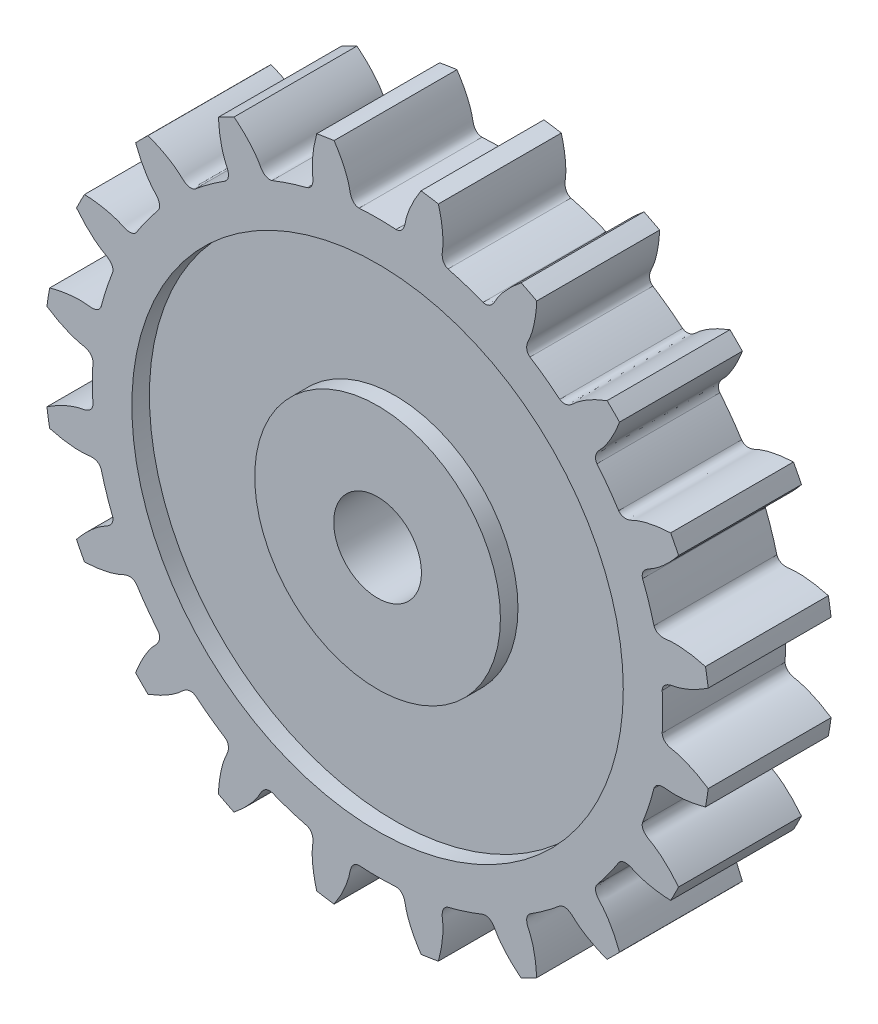
SolidWorks part; units mm, degrees
ref_plane "Alzado" through (0, 0, 0) normal (0, 0, 1) x (1, 0, 0)
ref_plane "Planta" through (0, 0, 0) normal (0, 1, 0) x (1, 0, 0)
ref_plane "Vista lateral" through (0, 0, 0) normal (1, 0, 0) x (0, 0, -1)
sketch "Croquis1" plane through (0, 0, 0) normal (0, 0, 1) x (1, 0, 0)
  line L0 (0, 0) -> (0, 22.9877) construction
  line L1 (0, 0) -> (13.435, 13.435) construction
  circle A0 centre (0, 0) radius 14 construction
  circle A1 centre (0, 0) radius 19 construction
  arc A2 (6.0093, 15.098) -> (4.0127, 15.7468) centre (0, 0) ccw
  arc A3 (17.1503, 8.1773) -> (16.6963, 9.0683) centre (0, 0) ccw
  arc A4 (18.8378, 2.4774) -> (18.6814, 3.4651) centre (0, 0) ccw
  arc A5 (18.6814, -3.4651) -> (18.8378, -2.4774) centre (0, 0) ccw
  arc A6 (16.6963, -9.0683) -> (17.1503, -8.1773) centre (0, 0) ccw
  arc A7 (13.0768, -13.7839) -> (13.7839, -13.0768) centre (0, 0) ccw
  arc A8 (8.1773, -17.1503) -> (9.0683, -16.6963) centre (0, 0) ccw
  arc A9 (2.4774, -18.8378) -> (3.4651, -18.6814) centre (0, 0) ccw
  arc A10 (-3.4651, -18.6814) -> (-2.4774, -18.8378) centre (0, 0) ccw
  arc A11 (-9.0683, -16.6963) -> (-8.1773, -17.1503) centre (0, 0) ccw
  arc A12 (-13.7839, -13.0768) -> (-13.0768, -13.7839) centre (0, 0) ccw
  arc A13 (-17.1503, -8.1773) -> (-16.6963, -9.0683) centre (0, 0) ccw
  arc A14 (-18.8378, -2.4774) -> (-18.6814, -3.4651) centre (0, 0) ccw
  arc A15 (-18.6814, 3.4651) -> (-18.8378, 2.4774) centre (0, 0) ccw
  arc A16 (-16.6963, 9.0683) -> (-17.1503, 8.1773) centre (0, 0) ccw
  arc A17 (-13.0768, 13.7839) -> (-13.7839, 13.0768) centre (0, 0) ccw
  arc A18 (-8.1773, 17.1503) -> (-9.0683, 16.6963) centre (0, 0) ccw
  arc A19 (-2.4774, 18.8378) -> (-3.4651, 18.6814) centre (0, 0) ccw
  arc A20 (3.4651, 18.6814) -> (2.4774, 18.8378) centre (0, 0) ccw
  arc A21 (9.0683, 16.6963) -> (8.1773, 17.1503) centre (0, 0) ccw
  arc A22 (10.3808, 12.5021) -> (8.6824, 13.7361) centre (0, 0) ccw
  arc A23 (13.7361, 8.6824) -> (12.5021, 10.3808) centre (0, 0) ccw
  arc A24 (15.7468, 4.0127) -> (15.098, 6.0093) centre (0, 0) ccw
  arc A25 (16.2161, -1.0497) -> (16.2161, 1.0497) centre (0, 0) ccw
  arc A26 (15.098, -6.0093) -> (15.7468, -4.0127) centre (0, 0) ccw
  arc A27 (12.5021, -10.3808) -> (13.7361, -8.6824) centre (0, 0) ccw
  arc A28 (8.6824, -13.7361) -> (10.3808, -12.5021) centre (0, 0) ccw
  arc A29 (4.0127, -15.7468) -> (6.0093, -15.098) centre (0, 0) ccw
  arc A30 (-1.0497, -16.2161) -> (1.0497, -16.2161) centre (0, 0) ccw
  arc A31 (-6.0093, -15.098) -> (-4.0127, -15.7468) centre (0, 0) ccw
  arc A32 (-10.3808, -12.5021) -> (-8.6824, -13.7361) centre (0, 0) ccw
  arc A33 (-13.7361, -8.6824) -> (-12.5021, -10.3808) centre (0, 0) ccw
  arc A34 (-15.7468, -4.0127) -> (-15.098, -6.0093) centre (0, 0) ccw
  arc A35 (-16.2161, 1.0497) -> (-16.2161, -1.0497) centre (0, 0) ccw
  arc A36 (-15.098, 6.0093) -> (-15.7468, 4.0127) centre (0, 0) ccw
  arc A37 (-12.5021, 10.3808) -> (-13.7361, 8.6824) centre (0, 0) ccw
  arc A38 (-8.6824, 13.7361) -> (-10.3808, 12.5021) centre (0, 0) ccw
  arc A39 (-4.0127, 15.7468) -> (-6.0093, 15.098) centre (0, 0) ccw
  arc A40 (1.0497, 16.2161) -> (-1.0497, 16.2161) centre (0, 0) ccw
  circle A41 centre (0, 0) radius 2.5
  arc A114 (13.7839, 13.0768) -> (13.0768, 13.7839) centre (0, 0) ccw
  spline S0 degree 3 poles (16.6963, 9.0683) (16.527, 9.0609) (16.2672, 9.0419) (15.9256, 8.9993) (15.6776, 8.9589) (15.4527, 8.9136) (15.2508, 8.8651) (15.072, 8.815) (14.9159, 8.7649) (14.7823, 8.7166) (14.671, 8.6714) (14.5901, 8.6353) (14.5356, 8.6086) (14.4998, 8.5913) (14.4673, 8.5768) (14.4142, 8.5546) (14.3398, 8.5283) (14.2409, 8.5042) (14.1356, 8.4929) (14.0177, 8.5009) (13.8695, 8.5484) (13.7779, 8.6259) (13.7361, 8.6824) knots 0 0 0 0 0.158673 0.243949 0.322403 0.394035 0.458845 0.516832 0.567998 0.612341 0.649863 0.680562 0.695323 0.706671 0.717793 0.728713 0.760516 0.791693 0.823807 0.859359 0.901681 0.967655 0.967655 0.967655 0.967655
  spline S1 degree 3 poles (15.098, 6.0093) (15.0769, 6.0764) (15.068, 6.196) (15.1168, 6.3439) (15.1796, 6.444) (15.2507, 6.5225) (15.3282, 6.5883) (15.3933, 6.6331) (15.4424, 6.663) (15.4733, 6.6807) (15.5083, 6.6995) (15.5619, 6.7279) (15.6387, 6.7721) (15.7407, 6.8357) (15.8583, 6.9153) (15.9905, 7.0122) (16.1362, 7.1274) (16.2941, 7.2622) (16.4629, 7.4175) (16.6414, 7.5944) (16.8767, 7.8457) (17.0448, 8.0448) (17.1503, 8.1773) knots 0.032345 0.032345 0.032345 0.032345 0.098319 0.140641 0.176193 0.208307 0.239484 0.271287 0.282207 0.293329 0.304677 0.319438 0.350137 0.387659 0.432002 0.483168 0.541155 0.605965 0.677597 0.756051 0.841327 1 1 1 1
  spline S2 degree 3 poles (18.6814, 3.4651) (18.5181, 3.5103) (18.2651, 3.5726) (17.9271, 3.6375) (17.6787, 3.6758) (17.4508, 3.7022) (17.2438, 3.7184) (17.0583, 3.726) (16.8944, 3.7266) (16.7524, 3.7219) (16.6325, 3.7134) (16.5444, 3.7041) (16.4844, 3.6955) (16.445, 3.6901) (16.4096, 3.6864) (16.3523, 3.6817) (16.2733, 3.6796) (16.1719, 3.6873) (16.0682, 3.709) (15.9586, 3.7532) (15.8322, 3.8441) (15.7691, 3.9461) (15.7468, 4.0127) knots 0 0 0 0 0.158673 0.243949 0.322403 0.394035 0.458845 0.516832 0.567998 0.612341 0.649863 0.680562 0.695323 0.706671 0.717793 0.728713 0.760516 0.791693 0.823807 0.859359 0.901681 0.967655 0.967655 0.967655 0.967655
  spline S3 degree 3 poles (16.2161, 1.0497) (16.2167, 1.1199) (16.2452, 1.2365) (16.3373, 1.362) (16.4279, 1.4378) (16.5198, 1.4905) (16.6139, 1.5292) (16.6896, 1.5516) (16.7456, 1.5649) (16.7805, 1.5723) (16.8196, 1.5793) (16.8793, 1.5897) (16.966, 1.608) (17.0826, 1.637) (17.2191, 1.6764) (17.3748, 1.7276) (17.5489, 1.7922) (17.7407, 1.8716) (17.9493, 1.9672) (18.1737, 2.0803) (18.4751, 2.2465) (18.6965, 2.3839) (18.8378, 2.4774) knots 0.032345 0.032345 0.032345 0.032345 0.098319 0.140641 0.176193 0.208307 0.239484 0.271287 0.282207 0.293329 0.304677 0.319438 0.350137 0.387659 0.432002 0.483168 0.541155 0.605965 0.677597 0.756051 0.841327 1 1 1 1
  spline S4 degree 3 poles (18.8378, -2.4774) (18.6965, -2.3839) (18.4751, -2.2465) (18.1737, -2.0803) (17.9493, -1.9672) (17.7407, -1.8716) (17.5489, -1.7922) (17.3748, -1.7276) (17.2191, -1.6764) (17.0826, -1.637) (16.966, -1.608) (16.8793, -1.5897) (16.8196, -1.5793) (16.7805, -1.5723) (16.7456, -1.5649) (16.6896, -1.5516) (16.6139, -1.5292) (16.5198, -1.4905) (16.4279, -1.4378) (16.3373, -1.362) (16.2452, -1.2365) (16.2167, -1.1199) (16.2161, -1.0497) knots 0 0 0 0 0.158673 0.243949 0.322403 0.394035 0.458845 0.516832 0.567998 0.612341 0.649863 0.680562 0.695323 0.706671 0.717793 0.728713 0.760516 0.791693 0.823807 0.859359 0.901681 0.967655 0.967655 0.967655 0.967655
  spline S5 degree 3 poles (15.7468, -4.0127) (15.7691, -3.9461) (15.8322, -3.8441) (15.9586, -3.7532) (16.0682, -3.709) (16.1719, -3.6873) (16.2733, -3.6796) (16.3523, -3.6817) (16.4096, -3.6864) (16.445, -3.6901) (16.4844, -3.6955) (16.5444, -3.7041) (16.6325, -3.7134) (16.7524, -3.7219) (16.8944, -3.7266) (17.0583, -3.726) (17.2438, -3.7184) (17.4508, -3.7022) (17.6787, -3.6758) (17.9271, -3.6375) (18.2651, -3.5726) (18.5181, -3.5103) (18.6814, -3.4651) knots 0.032345 0.032345 0.032345 0.032345 0.098319 0.140641 0.176193 0.208307 0.239484 0.271287 0.282207 0.293329 0.304677 0.319438 0.350137 0.387659 0.432002 0.483168 0.541155 0.605965 0.677597 0.756051 0.841327 1 1 1 1
  spline S6 degree 3 poles (17.1503, -8.1773) (17.0448, -8.0448) (16.8767, -7.8457) (16.6414, -7.5944) (16.4629, -7.4175) (16.2941, -7.2622) (16.1362, -7.1274) (15.9905, -7.0122) (15.8583, -6.9153) (15.7407, -6.8357) (15.6387, -6.7721) (15.5619, -6.7279) (15.5083, -6.6995) (15.4733, -6.6807) (15.4424, -6.663) (15.3933, -6.6331) (15.3282, -6.5883) (15.2507, -6.5225) (15.1796, -6.444) (15.1168, -6.3439) (15.068, -6.196) (15.0769, -6.0764) (15.098, -6.0093) knots 0 0 0 0 0.158673 0.243949 0.322403 0.394035 0.458845 0.516832 0.567998 0.612341 0.649863 0.680562 0.695323 0.706671 0.717793 0.728713 0.760516 0.791693 0.823807 0.859359 0.901681 0.967655 0.967655 0.967655 0.967655
  spline S7 degree 3 poles (13.7361, -8.6824) (13.7779, -8.6259) (13.8695, -8.5484) (14.0177, -8.5009) (14.1356, -8.4929) (14.2409, -8.5042) (14.3398, -8.5283) (14.4142, -8.5546) (14.4673, -8.5768) (14.4998, -8.5913) (14.5356, -8.6086) (14.5901, -8.6353) (14.671, -8.6714) (14.7823, -8.7166) (14.9159, -8.7649) (15.072, -8.815) (15.2508, -8.8651) (15.4527, -8.9136) (15.6776, -8.9589) (15.9256, -8.9993) (16.2672, -9.0419) (16.527, -9.0609) (16.6963, -9.0683) knots 0.032345 0.032345 0.032345 0.032345 0.098319 0.140641 0.176193 0.208307 0.239484 0.271287 0.282207 0.293329 0.304677 0.319438 0.350137 0.387659 0.432002 0.483168 0.541155 0.605965 0.677597 0.756051 0.841327 1 1 1 1
  spline S8 degree 3 poles (13.7839, -13.0768) (13.7246, -12.9182) (13.6262, -12.6769) (13.4801, -12.3652) (13.365, -12.1418) (13.2525, -11.9419) (13.1439, -11.7649) (13.041, -11.6103) (12.9452, -11.4774) (12.8579, -11.3653) (12.7806, -11.2733) (12.7212, -11.2075) (12.679, -11.164) (12.6515, -11.1353) (12.6276, -11.1088) (12.5902, -11.0652) (12.5421, -11.0025) (12.4887, -10.916) (12.4453, -10.8193) (12.4166, -10.7047) (12.4159, -10.5491) (12.4613, -10.438) (12.5021, -10.3808) knots 0 0 0 0 0.158673 0.243949 0.322403 0.394035 0.458845 0.516832 0.567998 0.612341 0.649863 0.680562 0.695323 0.706671 0.717793 0.728713 0.760516 0.791693 0.823807 0.859359 0.901681 0.967655 0.967655 0.967655 0.967655
  spline S9 degree 3 poles (10.3808, -12.5021) (10.438, -12.4613) (10.5491, -12.4159) (10.7047, -12.4166) (10.8193, -12.4453) (10.916, -12.4887) (11.0025, -12.5421) (11.0652, -12.5902) (11.1088, -12.6276) (11.1353, -12.6515) (11.164, -12.679) (11.2075, -12.7212) (11.2733, -12.7806) (11.3653, -12.8579) (11.4774, -12.9452) (11.6103, -13.041) (11.7649, -13.1439) (11.9419, -13.2525) (12.1418, -13.365) (12.3652, -13.4801) (12.6769, -13.6262) (12.9182, -13.7246) (13.0768, -13.7839) knots 0.032345 0.032345 0.032345 0.032345 0.098319 0.140641 0.176193 0.208307 0.239484 0.271287 0.282207 0.293329 0.304677 0.319438 0.350137 0.387659 0.432002 0.483168 0.541155 0.605965 0.677597 0.756051 0.841327 1 1 1 1
  spline S10 degree 3 poles (9.0683, -16.6963) (9.0609, -16.527) (9.0419, -16.2672) (8.9993, -15.9256) (8.9589, -15.6776) (8.9136, -15.4527) (8.8651, -15.2508) (8.815, -15.072) (8.7649, -14.9159) (8.7166, -14.7823) (8.6714, -14.671) (8.6353, -14.5901) (8.6086, -14.5356) (8.5913, -14.4998) (8.5768, -14.4673) (8.5546, -14.4142) (8.5283, -14.3398) (8.5042, -14.2409) (8.4929, -14.1356) (8.5009, -14.0177) (8.5484, -13.8695) (8.6259, -13.7779) (8.6824, -13.7361) knots 0 0 0 0 0.158673 0.243949 0.322403 0.394035 0.458845 0.516832 0.567998 0.612341 0.649863 0.680562 0.695323 0.706671 0.717793 0.728713 0.760516 0.791693 0.823807 0.859359 0.901681 0.967655 0.967655 0.967655 0.967655
  spline S11 degree 3 poles (6.0093, -15.098) (6.0764, -15.0769) (6.196, -15.068) (6.3439, -15.1168) (6.444, -15.1796) (6.5225, -15.2507) (6.5883, -15.3282) (6.6331, -15.3933) (6.663, -15.4424) (6.6807, -15.4733) (6.6995, -15.5083) (6.7279, -15.5619) (6.7721, -15.6387) (6.8357, -15.7407) (6.9153, -15.8583) (7.0122, -15.9905) (7.1274, -16.1362) (7.2622, -16.2941) (7.4175, -16.4629) (7.5944, -16.6414) (7.8457, -16.8767) (8.0448, -17.0448) (8.1773, -17.1503) knots 0.032345 0.032345 0.032345 0.032345 0.098319 0.140641 0.176193 0.208307 0.239484 0.271287 0.282207 0.293329 0.304677 0.319438 0.350137 0.387659 0.432002 0.483168 0.541155 0.605965 0.677597 0.756051 0.841327 1 1 1 1
  spline S12 degree 3 poles (3.4651, -18.6814) (3.5103, -18.5181) (3.5726, -18.2651) (3.6375, -17.9271) (3.6758, -17.6787) (3.7022, -17.4508) (3.7184, -17.2438) (3.726, -17.0583) (3.7266, -16.8944) (3.7219, -16.7524) (3.7134, -16.6325) (3.7041, -16.5444) (3.6955, -16.4844) (3.6901, -16.445) (3.6864, -16.4096) (3.6817, -16.3523) (3.6796, -16.2733) (3.6873, -16.1719) (3.709, -16.0682) (3.7532, -15.9586) (3.8441, -15.8322) (3.9461, -15.7691) (4.0127, -15.7468) knots 0 0 0 0 0.158673 0.243949 0.322403 0.394035 0.458845 0.516832 0.567998 0.612341 0.649863 0.680562 0.695323 0.706671 0.717793 0.728713 0.760516 0.791693 0.823807 0.859359 0.901681 0.967655 0.967655 0.967655 0.967655
  spline S13 degree 3 poles (1.0497, -16.2161) (1.1199, -16.2167) (1.2365, -16.2452) (1.362, -16.3373) (1.4378, -16.4279) (1.4905, -16.5198) (1.5292, -16.6139) (1.5516, -16.6896) (1.5649, -16.7456) (1.5723, -16.7805) (1.5793, -16.8196) (1.5897, -16.8793) (1.608, -16.966) (1.637, -17.0826) (1.6764, -17.2191) (1.7276, -17.3748) (1.7922, -17.5489) (1.8716, -17.7407) (1.9672, -17.9493) (2.0803, -18.1737) (2.2465, -18.4751) (2.3839, -18.6965) (2.4774, -18.8378) knots 0.032345 0.032345 0.032345 0.032345 0.098319 0.140641 0.176193 0.208307 0.239484 0.271287 0.282207 0.293329 0.304677 0.319438 0.350137 0.387659 0.432002 0.483168 0.541155 0.605965 0.677597 0.756051 0.841327 1 1 1 1
  spline S14 degree 3 poles (-2.4774, -18.8378) (-2.3839, -18.6965) (-2.2465, -18.4751) (-2.0803, -18.1737) (-1.9672, -17.9493) (-1.8716, -17.7407) (-1.7922, -17.5489) (-1.7276, -17.3748) (-1.6764, -17.2191) (-1.637, -17.0826) (-1.608, -16.966) (-1.5897, -16.8793) (-1.5793, -16.8196) (-1.5723, -16.7805) (-1.5649, -16.7456) (-1.5516, -16.6896) (-1.5292, -16.6139) (-1.4905, -16.5198) (-1.4378, -16.4279) (-1.362, -16.3373) (-1.2365, -16.2452) (-1.1199, -16.2167) (-1.0497, -16.2161) knots 0 0 0 0 0.158673 0.243949 0.322403 0.394035 0.458845 0.516832 0.567998 0.612341 0.649863 0.680562 0.695323 0.706671 0.717793 0.728713 0.760516 0.791693 0.823807 0.859359 0.901681 0.967655 0.967655 0.967655 0.967655
  spline S15 degree 3 poles (-4.0127, -15.7468) (-3.9461, -15.7691) (-3.8441, -15.8322) (-3.7532, -15.9586) (-3.709, -16.0682) (-3.6873, -16.1719) (-3.6796, -16.2733) (-3.6817, -16.3523) (-3.6864, -16.4096) (-3.6901, -16.445) (-3.6955, -16.4844) (-3.7041, -16.5444) (-3.7134, -16.6325) (-3.7219, -16.7524) (-3.7266, -16.8944) (-3.726, -17.0583) (-3.7184, -17.2438) (-3.7022, -17.4508) (-3.6758, -17.6787) (-3.6375, -17.9271) (-3.5726, -18.2651) (-3.5103, -18.5181) (-3.4651, -18.6814) knots 0.032345 0.032345 0.032345 0.032345 0.098319 0.140641 0.176193 0.208307 0.239484 0.271287 0.282207 0.293329 0.304677 0.319438 0.350137 0.387659 0.432002 0.483168 0.541155 0.605965 0.677597 0.756051 0.841327 1 1 1 1
  spline S16 degree 3 poles (-8.1773, -17.1503) (-8.0448, -17.0448) (-7.8457, -16.8767) (-7.5944, -16.6414) (-7.4175, -16.4629) (-7.2622, -16.2941) (-7.1274, -16.1362) (-7.0122, -15.9905) (-6.9153, -15.8583) (-6.8357, -15.7407) (-6.7721, -15.6387) (-6.7279, -15.5619) (-6.6995, -15.5083) (-6.6807, -15.4733) (-6.663, -15.4424) (-6.6331, -15.3933) (-6.5883, -15.3282) (-6.5225, -15.2507) (-6.444, -15.1796) (-6.3439, -15.1168) (-6.196, -15.068) (-6.0764, -15.0769) (-6.0093, -15.098) knots 0 0 0 0 0.158673 0.243949 0.322403 0.394035 0.458845 0.516832 0.567998 0.612341 0.649863 0.680562 0.695323 0.706671 0.717793 0.728713 0.760516 0.791693 0.823807 0.859359 0.901681 0.967655 0.967655 0.967655 0.967655
  spline S17 degree 3 poles (-8.6824, -13.7361) (-8.6259, -13.7779) (-8.5484, -13.8695) (-8.5009, -14.0177) (-8.4929, -14.1356) (-8.5042, -14.2409) (-8.5283, -14.3398) (-8.5546, -14.4142) (-8.5768, -14.4673) (-8.5913, -14.4998) (-8.6086, -14.5356) (-8.6353, -14.5901) (-8.6714, -14.671) (-8.7166, -14.7823) (-8.7649, -14.9159) (-8.815, -15.072) (-8.8651, -15.2508) (-8.9136, -15.4527) (-8.9589, -15.6776) (-8.9993, -15.9256) (-9.0419, -16.2672) (-9.0609, -16.527) (-9.0683, -16.6963) knots 0.032345 0.032345 0.032345 0.032345 0.098319 0.140641 0.176193 0.208307 0.239484 0.271287 0.282207 0.293329 0.304677 0.319438 0.350137 0.387659 0.432002 0.483168 0.541155 0.605965 0.677597 0.756051 0.841327 1 1 1 1
  spline S18 degree 3 poles (-13.0768, -13.7839) (-12.9182, -13.7246) (-12.6769, -13.6262) (-12.3652, -13.4801) (-12.1418, -13.365) (-11.9419, -13.2525) (-11.7649, -13.1439) (-11.6103, -13.041) (-11.4774, -12.9452) (-11.3653, -12.8579) (-11.2733, -12.7806) (-11.2075, -12.7212) (-11.164, -12.679) (-11.1353, -12.6515) (-11.1088, -12.6276) (-11.0652, -12.5902) (-11.0025, -12.5421) (-10.916, -12.4887) (-10.8193, -12.4453) (-10.7047, -12.4166) (-10.5491, -12.4159) (-10.438, -12.4613) (-10.3808, -12.5021) knots 0 0 0 0 0.158673 0.243949 0.322403 0.394035 0.458845 0.516832 0.567998 0.612341 0.649863 0.680562 0.695323 0.706671 0.717793 0.728713 0.760516 0.791693 0.823807 0.859359 0.901681 0.967655 0.967655 0.967655 0.967655
  spline S19 degree 3 poles (-12.5021, -10.3808) (-12.4613, -10.438) (-12.4159, -10.5491) (-12.4166, -10.7047) (-12.4453, -10.8193) (-12.4887, -10.916) (-12.5421, -11.0025) (-12.5902, -11.0652) (-12.6276, -11.1088) (-12.6515, -11.1353) (-12.679, -11.164) (-12.7212, -11.2075) (-12.7806, -11.2733) (-12.8579, -11.3653) (-12.9452, -11.4774) (-13.041, -11.6103) (-13.1439, -11.7649) (-13.2525, -11.9419) (-13.365, -12.1418) (-13.4801, -12.3652) (-13.6262, -12.6769) (-13.7246, -12.9182) (-13.7839, -13.0768) knots 0.032345 0.032345 0.032345 0.032345 0.098319 0.140641 0.176193 0.208307 0.239484 0.271287 0.282207 0.293329 0.304677 0.319438 0.350137 0.387659 0.432002 0.483168 0.541155 0.605965 0.677597 0.756051 0.841327 1 1 1 1
  spline S20 degree 3 poles (-16.6963, -9.0683) (-16.527, -9.0609) (-16.2672, -9.0419) (-15.9256, -8.9993) (-15.6776, -8.9589) (-15.4527, -8.9136) (-15.2508, -8.8651) (-15.072, -8.815) (-14.9159, -8.7649) (-14.7823, -8.7166) (-14.671, -8.6714) (-14.5901, -8.6353) (-14.5356, -8.6086) (-14.4998, -8.5913) (-14.4673, -8.5768) (-14.4142, -8.5546) (-14.3398, -8.5283) (-14.2409, -8.5042) (-14.1356, -8.4929) (-14.0177, -8.5009) (-13.8695, -8.5484) (-13.7779, -8.6259) (-13.7361, -8.6824) knots 0 0 0 0 0.158673 0.243949 0.322403 0.394035 0.458845 0.516832 0.567998 0.612341 0.649863 0.680562 0.695323 0.706671 0.717793 0.728713 0.760516 0.791693 0.823807 0.859359 0.901681 0.967655 0.967655 0.967655 0.967655
  spline S21 degree 3 poles (-15.098, -6.0093) (-15.0769, -6.0764) (-15.068, -6.196) (-15.1168, -6.3439) (-15.1796, -6.444) (-15.2507, -6.5225) (-15.3282, -6.5883) (-15.3933, -6.6331) (-15.4424, -6.663) (-15.4733, -6.6807) (-15.5083, -6.6995) (-15.5619, -6.7279) (-15.6387, -6.7721) (-15.7407, -6.8357) (-15.8583, -6.9153) (-15.9905, -7.0122) (-16.1362, -7.1274) (-16.2941, -7.2622) (-16.4629, -7.4175) (-16.6414, -7.5944) (-16.8767, -7.8457) (-17.0448, -8.0448) (-17.1503, -8.1773) knots 0.032345 0.032345 0.032345 0.032345 0.098319 0.140641 0.176193 0.208307 0.239484 0.271287 0.282207 0.293329 0.304677 0.319438 0.350137 0.387659 0.432002 0.483168 0.541155 0.605965 0.677597 0.756051 0.841327 1 1 1 1
  spline S22 degree 3 poles (-18.6814, -3.4651) (-18.5181, -3.5103) (-18.2651, -3.5726) (-17.9271, -3.6375) (-17.6787, -3.6758) (-17.4508, -3.7022) (-17.2438, -3.7184) (-17.0583, -3.726) (-16.8944, -3.7266) (-16.7524, -3.7219) (-16.6325, -3.7134) (-16.5444, -3.7041) (-16.4844, -3.6955) (-16.445, -3.6901) (-16.4096, -3.6864) (-16.3523, -3.6817) (-16.2733, -3.6796) (-16.1719, -3.6873) (-16.0682, -3.709) (-15.9586, -3.7532) (-15.8322, -3.8441) (-15.7691, -3.9461) (-15.7468, -4.0127) knots 0 0 0 0 0.158673 0.243949 0.322403 0.394035 0.458845 0.516832 0.567998 0.612341 0.649863 0.680562 0.695323 0.706671 0.717793 0.728713 0.760516 0.791693 0.823807 0.859359 0.901681 0.967655 0.967655 0.967655 0.967655
  spline S23 degree 3 poles (-16.2161, -1.0497) (-16.2167, -1.1199) (-16.2452, -1.2365) (-16.3373, -1.362) (-16.4279, -1.4378) (-16.5198, -1.4905) (-16.6139, -1.5292) (-16.6896, -1.5516) (-16.7456, -1.5649) (-16.7805, -1.5723) (-16.8196, -1.5793) (-16.8793, -1.5897) (-16.966, -1.608) (-17.0826, -1.637) (-17.2191, -1.6764) (-17.3748, -1.7276) (-17.5489, -1.7922) (-17.7407, -1.8716) (-17.9493, -1.9672) (-18.1737, -2.0803) (-18.4751, -2.2465) (-18.6965, -2.3839) (-18.8378, -2.4774) knots 0.032345 0.032345 0.032345 0.032345 0.098319 0.140641 0.176193 0.208307 0.239484 0.271287 0.282207 0.293329 0.304677 0.319438 0.350137 0.387659 0.432002 0.483168 0.541155 0.605965 0.677597 0.756051 0.841327 1 1 1 1
  spline S24 degree 3 poles (-18.8378, 2.4774) (-18.6965, 2.3839) (-18.4751, 2.2465) (-18.1737, 2.0803) (-17.9493, 1.9672) (-17.7407, 1.8716) (-17.5489, 1.7922) (-17.3748, 1.7276) (-17.2191, 1.6764) (-17.0826, 1.637) (-16.966, 1.608) (-16.8793, 1.5897) (-16.8196, 1.5793) (-16.7805, 1.5723) (-16.7456, 1.5649) (-16.6896, 1.5516) (-16.6139, 1.5292) (-16.5198, 1.4905) (-16.4279, 1.4378) (-16.3373, 1.362) (-16.2452, 1.2365) (-16.2167, 1.1199) (-16.2161, 1.0497) knots 0 0 0 0 0.158673 0.243949 0.322403 0.394035 0.458845 0.516832 0.567998 0.612341 0.649863 0.680562 0.695323 0.706671 0.717793 0.728713 0.760516 0.791693 0.823807 0.859359 0.901681 0.967655 0.967655 0.967655 0.967655
  spline S25 degree 3 poles (-15.7468, 4.0127) (-15.7691, 3.9461) (-15.8322, 3.8441) (-15.9586, 3.7532) (-16.0682, 3.709) (-16.1719, 3.6873) (-16.2733, 3.6796) (-16.3523, 3.6817) (-16.4096, 3.6864) (-16.445, 3.6901) (-16.4844, 3.6955) (-16.5444, 3.7041) (-16.6325, 3.7134) (-16.7524, 3.7219) (-16.8944, 3.7266) (-17.0583, 3.726) (-17.2438, 3.7184) (-17.4508, 3.7022) (-17.6787, 3.6758) (-17.9271, 3.6375) (-18.2651, 3.5726) (-18.5181, 3.5103) (-18.6814, 3.4651) knots 0.032345 0.032345 0.032345 0.032345 0.098319 0.140641 0.176193 0.208307 0.239484 0.271287 0.282207 0.293329 0.304677 0.319438 0.350137 0.387659 0.432002 0.483168 0.541155 0.605965 0.677597 0.756051 0.841327 1 1 1 1
  spline S26 degree 3 poles (-17.1503, 8.1773) (-17.0448, 8.0448) (-16.8767, 7.8457) (-16.6414, 7.5944) (-16.4629, 7.4175) (-16.2941, 7.2622) (-16.1362, 7.1274) (-15.9905, 7.0122) (-15.8583, 6.9153) (-15.7407, 6.8357) (-15.6387, 6.7721) (-15.5619, 6.7279) (-15.5083, 6.6995) (-15.4733, 6.6807) (-15.4424, 6.663) (-15.3933, 6.6331) (-15.3282, 6.5883) (-15.2507, 6.5225) (-15.1796, 6.444) (-15.1168, 6.3439) (-15.068, 6.196) (-15.0769, 6.0764) (-15.098, 6.0093) knots 0 0 0 0 0.158673 0.243949 0.322403 0.394035 0.458845 0.516832 0.567998 0.612341 0.649863 0.680562 0.695323 0.706671 0.717793 0.728713 0.760516 0.791693 0.823807 0.859359 0.901681 0.967655 0.967655 0.967655 0.967655
  spline S27 degree 3 poles (-13.7361, 8.6824) (-13.7779, 8.6259) (-13.8695, 8.5484) (-14.0177, 8.5009) (-14.1356, 8.4929) (-14.2409, 8.5042) (-14.3398, 8.5283) (-14.4142, 8.5546) (-14.4673, 8.5768) (-14.4998, 8.5913) (-14.5356, 8.6086) (-14.5901, 8.6353) (-14.671, 8.6714) (-14.7823, 8.7166) (-14.9159, 8.7649) (-15.072, 8.815) (-15.2508, 8.8651) (-15.4527, 8.9136) (-15.6776, 8.9589) (-15.9256, 8.9993) (-16.2672, 9.0419) (-16.527, 9.0609) (-16.6963, 9.0683) knots 0.032345 0.032345 0.032345 0.032345 0.098319 0.140641 0.176193 0.208307 0.239484 0.271287 0.282207 0.293329 0.304677 0.319438 0.350137 0.387659 0.432002 0.483168 0.541155 0.605965 0.677597 0.756051 0.841327 1 1 1 1
  spline S28 degree 3 poles (-13.7839, 13.0768) (-13.7246, 12.9182) (-13.6262, 12.6769) (-13.4801, 12.3652) (-13.365, 12.1418) (-13.2525, 11.9419) (-13.1439, 11.7649) (-13.041, 11.6103) (-12.9452, 11.4774) (-12.8579, 11.3653) (-12.7806, 11.2733) (-12.7212, 11.2075) (-12.679, 11.164) (-12.6515, 11.1353) (-12.6276, 11.1088) (-12.5902, 11.0652) (-12.5421, 11.0025) (-12.4887, 10.916) (-12.4453, 10.8193) (-12.4166, 10.7047) (-12.4159, 10.5491) (-12.4613, 10.438) (-12.5021, 10.3808) knots 0 0 0 0 0.158673 0.243949 0.322403 0.394035 0.458845 0.516832 0.567998 0.612341 0.649863 0.680562 0.695323 0.706671 0.717793 0.728713 0.760516 0.791693 0.823807 0.859359 0.901681 0.967655 0.967655 0.967655 0.967655
  spline S29 degree 3 poles (-10.3808, 12.5021) (-10.438, 12.4613) (-10.5491, 12.4159) (-10.7047, 12.4166) (-10.8193, 12.4453) (-10.916, 12.4887) (-11.0025, 12.5421) (-11.0652, 12.5902) (-11.1088, 12.6276) (-11.1353, 12.6515) (-11.164, 12.679) (-11.2075, 12.7212) (-11.2733, 12.7806) (-11.3653, 12.8579) (-11.4774, 12.9452) (-11.6103, 13.041) (-11.7649, 13.1439) (-11.9419, 13.2525) (-12.1418, 13.365) (-12.3652, 13.4801) (-12.6769, 13.6262) (-12.9182, 13.7246) (-13.0768, 13.7839) knots 0.032345 0.032345 0.032345 0.032345 0.098319 0.140641 0.176193 0.208307 0.239484 0.271287 0.282207 0.293329 0.304677 0.319438 0.350137 0.387659 0.432002 0.483168 0.541155 0.605965 0.677597 0.756051 0.841327 1 1 1 1
  spline S30 degree 3 poles (-9.0683, 16.6963) (-9.0609, 16.527) (-9.0419, 16.2672) (-8.9993, 15.9256) (-8.9589, 15.6776) (-8.9136, 15.4527) (-8.8651, 15.2508) (-8.815, 15.072) (-8.7649, 14.9159) (-8.7166, 14.7823) (-8.6714, 14.671) (-8.6353, 14.5901) (-8.6086, 14.5356) (-8.5913, 14.4998) (-8.5768, 14.4673) (-8.5546, 14.4142) (-8.5283, 14.3398) (-8.5042, 14.2409) (-8.4929, 14.1356) (-8.5009, 14.0177) (-8.5484, 13.8695) (-8.6259, 13.7779) (-8.6824, 13.7361) knots 0 0 0 0 0.158673 0.243949 0.322403 0.394035 0.458845 0.516832 0.567998 0.612341 0.649863 0.680562 0.695323 0.706671 0.717793 0.728713 0.760516 0.791693 0.823807 0.859359 0.901681 0.967655 0.967655 0.967655 0.967655
  spline S31 degree 3 poles (-6.0093, 15.098) (-6.0764, 15.0769) (-6.196, 15.068) (-6.3439, 15.1168) (-6.444, 15.1796) (-6.5225, 15.2507) (-6.5883, 15.3282) (-6.6331, 15.3933) (-6.663, 15.4424) (-6.6807, 15.4733) (-6.6995, 15.5083) (-6.7279, 15.5619) (-6.7721, 15.6387) (-6.8357, 15.7407) (-6.9153, 15.8583) (-7.0122, 15.9905) (-7.1274, 16.1362) (-7.2622, 16.2941) (-7.4175, 16.4629) (-7.5944, 16.6414) (-7.8457, 16.8767) (-8.0448, 17.0448) (-8.1773, 17.1503) knots 0.032345 0.032345 0.032345 0.032345 0.098319 0.140641 0.176193 0.208307 0.239484 0.271287 0.282207 0.293329 0.304677 0.319438 0.350137 0.387659 0.432002 0.483168 0.541155 0.605965 0.677597 0.756051 0.841327 1 1 1 1
  spline S32 degree 3 poles (-3.4651, 18.6814) (-3.5103, 18.5181) (-3.5726, 18.2651) (-3.6375, 17.9271) (-3.6758, 17.6787) (-3.7022, 17.4508) (-3.7184, 17.2438) (-3.726, 17.0583) (-3.7266, 16.8944) (-3.7219, 16.7524) (-3.7134, 16.6325) (-3.7041, 16.5444) (-3.6955, 16.4844) (-3.6901, 16.445) (-3.6864, 16.4096) (-3.6817, 16.3523) (-3.6796, 16.2733) (-3.6873, 16.1719) (-3.709, 16.0682) (-3.7532, 15.9586) (-3.8441, 15.8322) (-3.9461, 15.7691) (-4.0127, 15.7468) knots 0 0 0 0 0.158673 0.243949 0.322403 0.394035 0.458845 0.516832 0.567998 0.612341 0.649863 0.680562 0.695323 0.706671 0.717793 0.728713 0.760516 0.791693 0.823807 0.859359 0.901681 0.967655 0.967655 0.967655 0.967655
  spline S33 degree 3 poles (-1.0497, 16.2161) (-1.1199, 16.2167) (-1.2365, 16.2452) (-1.362, 16.3373) (-1.4378, 16.4279) (-1.4905, 16.5198) (-1.5292, 16.6139) (-1.5516, 16.6896) (-1.5649, 16.7456) (-1.5723, 16.7805) (-1.5793, 16.8196) (-1.5897, 16.8793) (-1.608, 16.966) (-1.637, 17.0826) (-1.6764, 17.2191) (-1.7276, 17.3748) (-1.7922, 17.5489) (-1.8716, 17.7407) (-1.9672, 17.9493) (-2.0803, 18.1737) (-2.2465, 18.4751) (-2.3839, 18.6965) (-2.4774, 18.8378) knots 0.032345 0.032345 0.032345 0.032345 0.098319 0.140641 0.176193 0.208307 0.239484 0.271287 0.282207 0.293329 0.304677 0.319438 0.350137 0.387659 0.432002 0.483168 0.541155 0.605965 0.677597 0.756051 0.841327 1 1 1 1
  spline S34 degree 3 poles (2.4774, 18.8378) (2.3839, 18.6965) (2.2465, 18.4751) (2.0803, 18.1737) (1.9672, 17.9493) (1.8716, 17.7407) (1.7922, 17.5489) (1.7276, 17.3748) (1.6764, 17.2191) (1.637, 17.0826) (1.608, 16.966) (1.5897, 16.8793) (1.5793, 16.8196) (1.5723, 16.7805) (1.5649, 16.7456) (1.5516, 16.6896) (1.5292, 16.6139) (1.4905, 16.5198) (1.4378, 16.4279) (1.362, 16.3373) (1.2365, 16.2452) (1.1199, 16.2167) (1.0497, 16.2161) knots 0 0 0 0 0.158673 0.243949 0.322403 0.394035 0.458845 0.516832 0.567998 0.612341 0.649863 0.680562 0.695323 0.706671 0.717793 0.728713 0.760516 0.791693 0.823807 0.859359 0.901681 0.967655 0.967655 0.967655 0.967655
  spline S35 degree 3 poles (4.0127, 15.7468) (3.9461, 15.7691) (3.8441, 15.8322) (3.7532, 15.9586) (3.709, 16.0682) (3.6873, 16.1719) (3.6796, 16.2733) (3.6817, 16.3523) (3.6864, 16.4096) (3.6901, 16.445) (3.6955, 16.4844) (3.7041, 16.5444) (3.7134, 16.6325) (3.7219, 16.7524) (3.7266, 16.8944) (3.726, 17.0583) (3.7184, 17.2438) (3.7022, 17.4508) (3.6758, 17.6787) (3.6375, 17.9271) (3.5726, 18.2651) (3.5103, 18.5181) (3.4651, 18.6814) knots 0.032345 0.032345 0.032345 0.032345 0.098319 0.140641 0.176193 0.208307 0.239484 0.271287 0.282207 0.293329 0.304677 0.319438 0.350137 0.387659 0.432002 0.483168 0.541155 0.605965 0.677597 0.756051 0.841327 1 1 1 1
  spline S36 degree 3 poles (8.1773, 17.1503) (8.0448, 17.0448) (7.8457, 16.8767) (7.5944, 16.6414) (7.4175, 16.4629) (7.2622, 16.2941) (7.1274, 16.1362) (7.0122, 15.9905) (6.9153, 15.8583) (6.8357, 15.7407) (6.7721, 15.6387) (6.7279, 15.5619) (6.6995, 15.5083) (6.6807, 15.4733) (6.663, 15.4424) (6.6331, 15.3933) (6.5883, 15.3282) (6.5225, 15.2507) (6.444, 15.1796) (6.3439, 15.1168) (6.196, 15.068) (6.0764, 15.0769) (6.0093, 15.098) knots 0 0 0 0 0.158673 0.243949 0.322403 0.394035 0.458845 0.516832 0.567998 0.612341 0.649863 0.680562 0.695323 0.706671 0.717793 0.728713 0.760516 0.791693 0.823807 0.859359 0.901681 0.967655 0.967655 0.967655 0.967655
  spline S37 degree 3 poles (8.6824, 13.7361) (8.6259, 13.7779) (8.5484, 13.8695) (8.5009, 14.0177) (8.4929, 14.1356) (8.5042, 14.2409) (8.5283, 14.3398) (8.5546, 14.4142) (8.5768, 14.4673) (8.5913, 14.4998) (8.6086, 14.5356) (8.6353, 14.5901) (8.6714, 14.671) (8.7166, 14.7823) (8.7649, 14.9159) (8.815, 15.072) (8.8651, 15.2508) (8.9136, 15.4527) (8.9589, 15.6776) (8.9993, 15.9256) (9.0419, 16.2672) (9.0609, 16.527) (9.0683, 16.6963) knots 0.032345 0.032345 0.032345 0.032345 0.098319 0.140641 0.176193 0.208307 0.239484 0.271287 0.282207 0.293329 0.304677 0.319438 0.350137 0.387659 0.432002 0.483168 0.541155 0.605965 0.677597 0.756051 0.841327 1 1 1 1
  spline S101 degree 3 poles (12.5021, 10.3808) (12.4613, 10.438) (12.4159, 10.5491) (12.4166, 10.7047) (12.4453, 10.8193) (12.4887, 10.916) (12.5421, 11.0025) (12.5902, 11.0652) (12.6276, 11.1088) (12.6515, 11.1353) (12.679, 11.164) (12.7212, 11.2075) (12.7806, 11.2733) (12.8579, 11.3653) (12.9452, 11.4774) (13.041, 11.6103) (13.1439, 11.7649) (13.2525, 11.9419) (13.365, 12.1418) (13.4801, 12.3652) (13.6262, 12.6769) (13.7246, 12.9182) (13.7839, 13.0768) knots 0.032345 0.032345 0.032345 0.032345 0.098319 0.140641 0.176193 0.208307 0.239484 0.271287 0.282207 0.293329 0.304677 0.319438 0.350137 0.387659 0.432002 0.483168 0.541155 0.605965 0.677597 0.756051 0.841327 1 1 1 1
  spline S102 degree 3 poles (13.0768, 13.7839) (12.9182, 13.7246) (12.6769, 13.6262) (12.3652, 13.4801) (12.1418, 13.365) (11.9419, 13.2525) (11.7649, 13.1439) (11.6103, 13.041) (11.4774, 12.9452) (11.3653, 12.8579) (11.2733, 12.7806) (11.2075, 12.7212) (11.164, 12.679) (11.1353, 12.6515) (11.1088, 12.6276) (11.0652, 12.5902) (11.0025, 12.5421) (10.916, 12.4887) (10.8193, 12.4453) (10.7047, 12.4166) (10.5491, 12.4159) (10.438, 12.4613) (10.3808, 12.5021) knots 0 0 0 0 0.158673 0.243949 0.322403 0.394035 0.458845 0.516832 0.567998 0.612341 0.649863 0.680562 0.695323 0.706671 0.717793 0.728713 0.760516 0.791693 0.823807 0.859359 0.901681 0.967655 0.967655 0.967655 0.967655
  dimension "D2" = 28
  dimension "D3" = 45
  dimension "D4" = 32.5
  dimension "D5" = 0.5
  dimension "D1" = 38
  dimension "D9" = 5
  dimension "D6" = 1.5
  dimension "D7" = 1.5
  dimension "D8" = 20
extrude "Saliente-Extruir1" add sketch "Croquis1" along normal blind 7
sketch "Croquis2" plane through (0, 0, 7) normal (0, 0, 1) x (1, 0, 0)
  circle A0 centre (0, 0) radius 14
  circle A1 centre (0, 0) radius 7
  dimension "D1" = 28
  dimension "D2" = 14
extrude "Cortar-Extruir1" cut sketch "Croquis2" against normal blind 1
sketch "Croquis3" plane through (0, 0, 0) normal (0, 0, -1) x (-1, 0, 0)
  circle A1 centre (0, 0) radius 7
  circle A2 centre (0, 0) radius 7
  circle A3 centre (0, 0) radius 14
  circle A4 centre (0, 0) radius 14
  dimension "D1" = 0
  dimension "D2" = 0
extrude "Cortar-Extruir2" cut sketch "Croquis3" against normal blind 1
